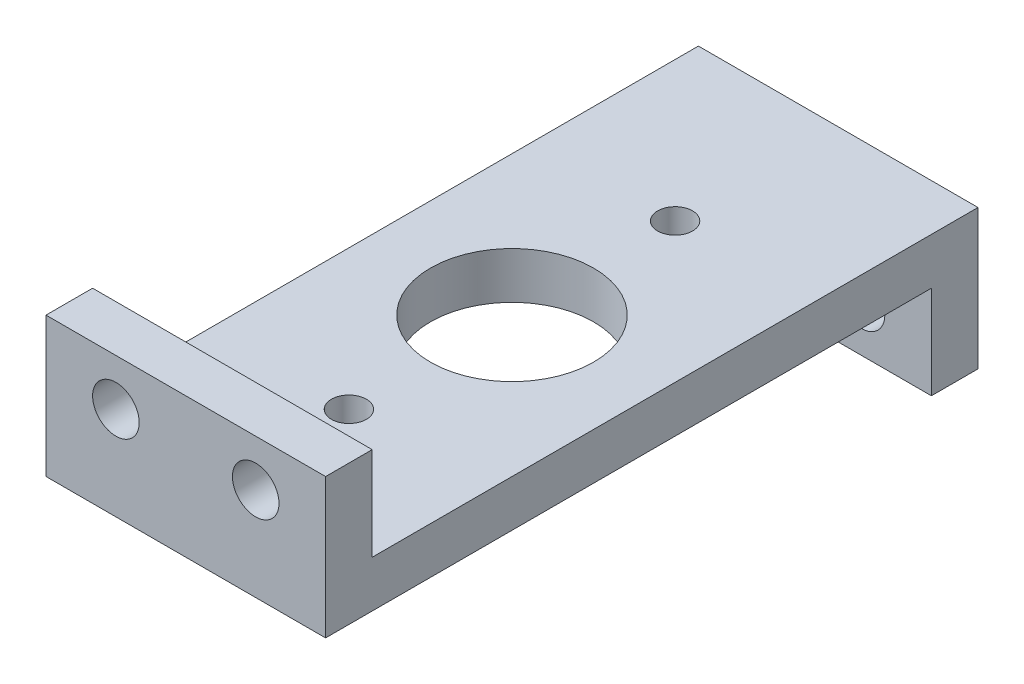
SolidWorks part; units mm, degrees
material "Alloy Steel"
ref_plane "Front Plane" through (0, 0, 0) normal (0, 0, 1) x (1, 0, 0)
ref_plane "Top Plane" through (0, 0, 0) normal (0, 1, 0) x (1, 0, 0)
ref_plane "Right Plane" through (0, 0, 0) normal (1, 0, 0) x (0, 0, -1)
sketch "Sketch2" plane through (0, 0, 0) normal (1, 0, 0) x (0, 0, -1)
  line L1 (-78.8186, -25.3345) -> (86.2814, -25.3345)
  line L2 (-78.8186, -25.3345) -> (-78.8186, -6.8759)
  line L3 (-66.1186, -12.6345) -> (98.9814, -12.6345)
  line L4 (98.9814, -25.3345) -> (98.9814, -12.6345)
  line L6 (-78.8186, -6.8759) -> (-78.8186, 12.7655)
  line L7 (-78.8186, 12.7655) -> (-66.1186, 12.7655)
  line L8 (-66.1186, -12.6345) -> (-66.1186, 12.7655)
  line L10 (98.9814, -25.3345) -> (98.9814, -50.7345)
  line L11 (98.9814, -50.7345) -> (86.2814, -50.7345)
  line L12 (86.2814, -25.3345) -> (86.2814, -50.7345)
  dimension "D1" = 177.8
  dimension "D2" = 12.7
  dimension "D3" = 38.1
  dimension "D4" = 12.7
  dimension "D5" = 38.1
  dimension "D6" = 12.7
extrude "Boss-Extrude1" add sketch "Sketch2" along normal blind 76.2
sketch "Sketch3" plane through (0, 0, -98.9814) normal (0, 0, -1) x (-1, 0, 0)
  line L0 (0, -50.7345) -> (0, -12.6345) construction
  line L1 (-76.2, -50.7345) -> (-76.2, -12.6345) construction
  line L2 (-76.2, -50.7345) -> (0, -50.7345) construction
  circle A0 centre (-57.15, -38.0345) radius 6.35
  circle A1 centre (-19.05, -38.0345) radius 6.35
  dimension "D1" = 12.7
  dimension "D2" = 19.05
  dimension "D3" = 19.05
  dimension "D4" = 12.7
extrude "Cut-Extrude1" cut sketch "Sketch3" against normal blind 76.2
sketch "Sketch4" plane through (0, 0, 66.1186) normal (0, 0, -1) x (-1, 0, 0)
  line L1 (-76.2, 12.7655) -> (0, 12.7655) construction
  line L2 (-76.2, -12.6345) -> (-76.2, 12.7655) construction
  circle A0 centre (-57.15, 0.0655) radius 6.35
  circle A1 centre (-19.05, 0.0655) radius 6.35
  dimension "D1" = 19.05
  dimension "D2" = 12.7
extrude "Cut-Extrude2" cut sketch "Sketch4" against normal blind 76.2
sketch "Sketch5" plane through (0, -12.6345, 0) normal (0, 1, 0) x (1, 0, 0)
  line L2 (76.2, 98.9814) -> (76.2, -66.1186) construction
  line L4 (76.2, -78.8186) -> (0, -78.8186) construction
  circle A0 centre (38.1, 10.0814) radius 22.225
  circle A1 centre (38.1, 54.5314) radius 4.7625
  circle A2 centre (38.1, -34.3686) radius 4.7625
  dimension "D3" = 44.45
  dimension "D4" = 9.525
  dimension "D1" = 44.45
  dimension "D5" = 38.1
  dimension "D6" = 88.9
extrude "Cut-Extrude3" cut sketch "Sketch5" against normal blind 76.2
